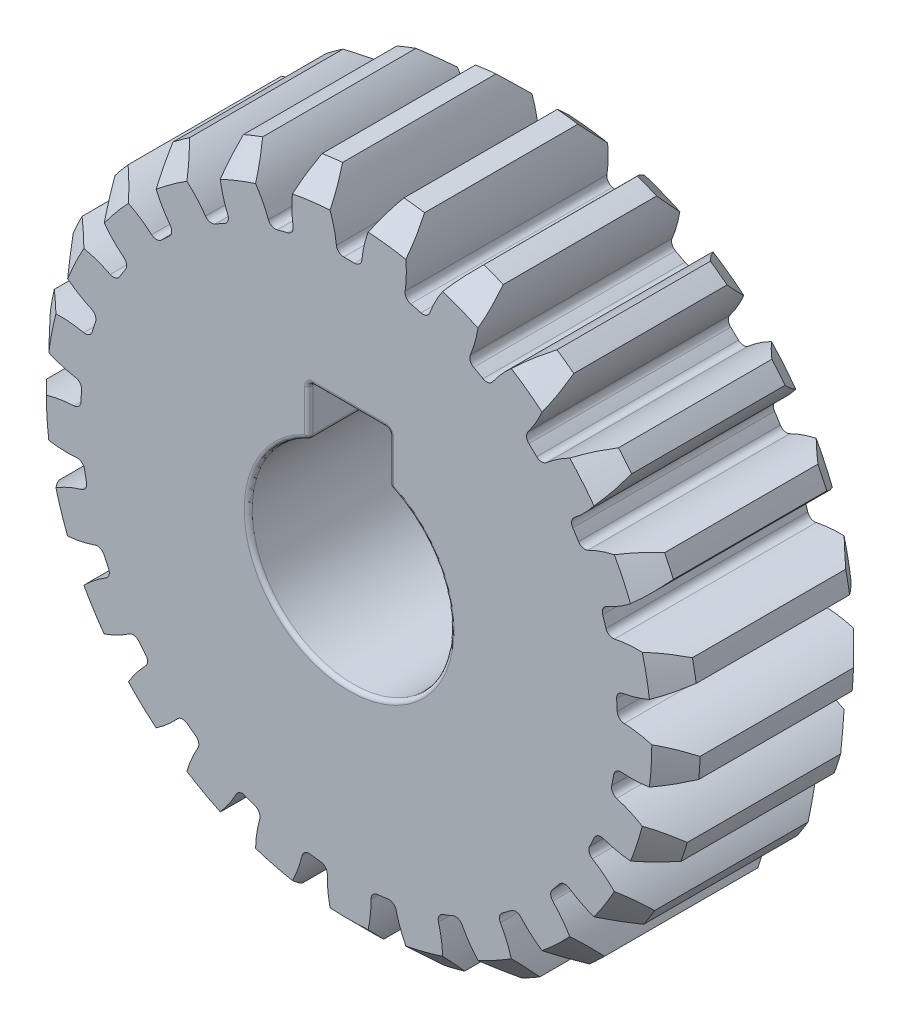
SolidWorks part; units mm, degrees
ref_plane "Front Plane" through (0, 0, 0) normal (0, 0, 1) x (1, 0, 0)
ref_plane "Top Plane" through (0, 0, 0) normal (0, 1, 0) x (1, 0, 0)
ref_plane "Right Plane" through (0, 0, 0) normal (1, 0, 0) x (0, 0, -1)
sketch "Sketch1" plane through (0, 0, 0) normal (0, 0, 1) x (1, 0, 0)
  circle A0 centre (0, 0) radius 15 construction
  circle A1 centre (0, 0) radius 16.2
  dimension "D1" = 30
  dimension "D2" = 32.4
extrude "Boss-Extrude1" add sketch "Sketch1" along normal mid plane 10
sketch "Sketch2" plane through (0, 0, 0) normal (0, 0, 1) x (1, 0, 0)
  line L0 (0, 0) -> (0, 16.2) construction
  line L1 (0, 0) -> (4.0288, 15.691) construction
  line L2 (0, 0) -> (2.0304, 16.0723) construction
  line L3 (-0.6052, 13.2862) -> (0, 0) construction
  line L4 (-0.9419, 14.9704) -> (0.9419, 14.9704) construction
  line L5 (0.9419, 14.9704) -> (2.8107, 14.7343) construction
  line L6 (-1.3683, 16.1421) -> (0, 12.3827) construction
  circle A0 centre (0, 0) radius 13.8 construction
  circle A2 centre (0, 0) radius 16.2 construction
  arc A3 (-1.5204, 16.1285) -> (-0.6052, 13.2862) centre (-6.2792, 13.0278) cw
  circle A4 centre (0, 0) radius 16.2 construction
  arc A5 (1.5204, 16.1285) -> (0.6052, 13.2862) centre (6.2792, 13.0278) ccw
  circle A6 centre (0, 0) radius 15 construction
  arc A7 (0.6052, 13.2862) -> (-0.6052, 13.2862) centre (0, 0) ccw
  arc A8 (1.5204, 16.1285) -> (-1.5204, 16.1285) centre (0, 0) ccw
  dimension "D1" = 14.4
  dimension "D2" = 2.4
  dimension "D4" = 20
  dimension "D3" = 0.5
extrude "Cut-Extrude1" cut sketch "Sketch2" against normal through all both and the other way through all contours A5 A8 A3 A7
fillet "Fillet1" radius 0.36 2 edges at (0.6052, 13.2862, 0) (-0.6052, 13.2862, 0)
chamfer "Chamfer1" distance 1.2 angle 45 2 edges at (0, -16.2, -5) (0, -16.2, 5)
pattern_circular "CirPattern1" count 25 over 360 about axis through (0, 0, 0) along (0, 0, 1) of "Fillet1", "Cut-Extrude1"
sketch "Sketch3" plane through (0, 0, 5) normal (0, 0, 1) x (1, 0, 0)
  line L2 (-2, 4.5826) -> (-2, 7)
  line L3 (-2, 7) -> (2, 7)
  line L4 (2, 4.5826) -> (2, 7)
  arc A0 (-2, 4.5826) -> (2, 4.5826) centre (0, 0) ccw
  point P3 (0, 5)
  point P5 (0, 7)
  dimension "D1" = 10
  dimension "D2" = 2
  dimension "D3" = 4
extrude "Cut-Extrude2" cut sketch "Sketch3" against normal through all
fillet "Fillet2" radius 0.2 12 edges at (0, -5, 5) (0, -5, -5) (-2, 4.5826, 0) (2, 4.5826, 0) (0, 7, -5) (0, 7, 5) (-2, 7, 0) (-2, 5.7913, -5) (-2, 5.7913, 5) (2, 5.7913, -5) (2, 7, 0) (2, 5.7913, 5)
sketch "Sketch5" plane through (0, 0, 0) normal (0, 0, 1) x (1, 0, 0)
  circle A0 centre (0, 0) radius 15
equation "\"Module\"= 1.2"
equation "\"Number of Teeth\"= 25'Number of Teeth"
equation "\"Pressure Angle\"= 20"
equation "\"D1@Sketch1\"=\"Module\" * \"Number of Teeth\""
equation "\"D2@Sketch1\"=( \"Number of Teeth\" + 2) * \"Module\""
equation "\"D1@Sketch2\"=360 / \"Number of Teeth\""
equation "\"D2@Sketch2\"= \"Module\" * 2"
equation "\"D4@Sketch2\"=\"Pressure Angle\""
equation "\"D1@Fillet1\"=0.3 * \"Module\""
equation "\"D1@CirPattern1\"= \"Number of Teeth\""
equation "\"D1@Chamfer1\"= \"Module\""
equation "\"Gear Thickness\"= 10"
equation "\"D1@Boss-Extrude1\"= \"Gear Thickness\""
